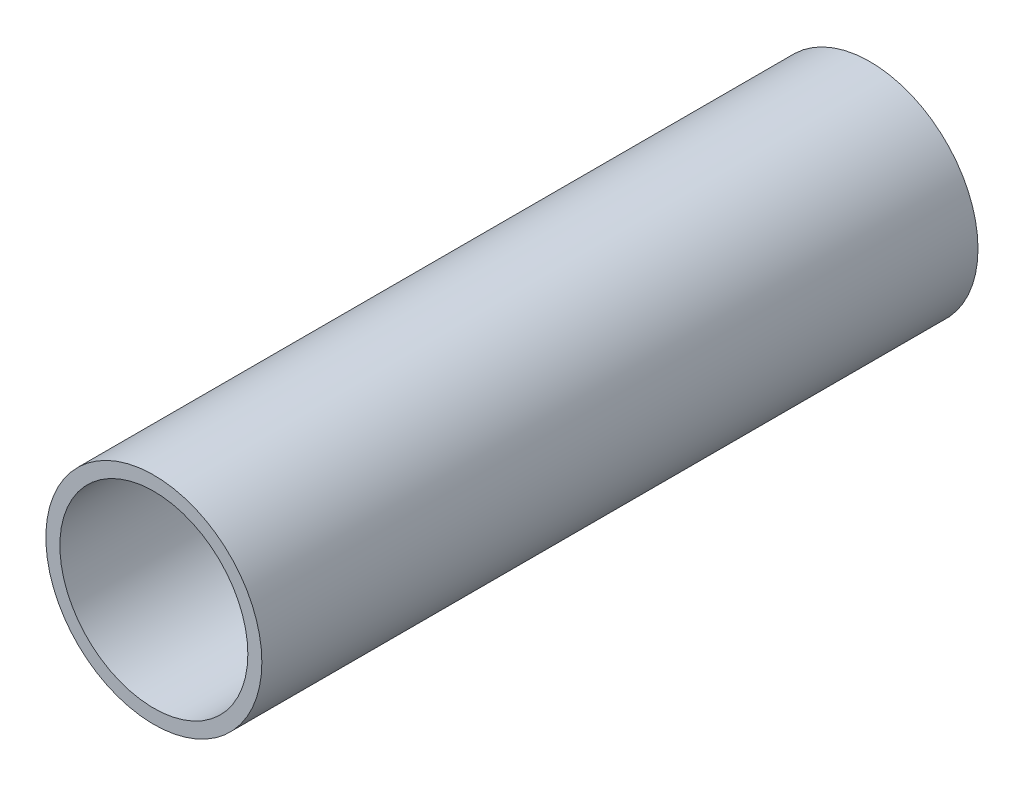
SolidWorks part; units mm, degrees
ref_plane "Front Plane" through (0, 0, 0) normal (0, 0, 1) x (1, 0, 0)
ref_plane "Top Plane" through (0, 0, 0) normal (0, 1, 0) x (1, 0, 0)
ref_plane "Right Plane" through (0, 0, 0) normal (1, 0, 0) x (0, 0, -1)
sketch "Sketch1" plane through (0, 0, 0) normal (0, 0, 1) x (1, 0, 0)
  circle A0 centre (0, 0) radius 30.1625
  dimension "Pipe OD" = 60.325
extrude "Extrude-Thin1" add sketch "Sketch1" along normal mid plane 200 thin thin type one direction reverse wall 3.9116
